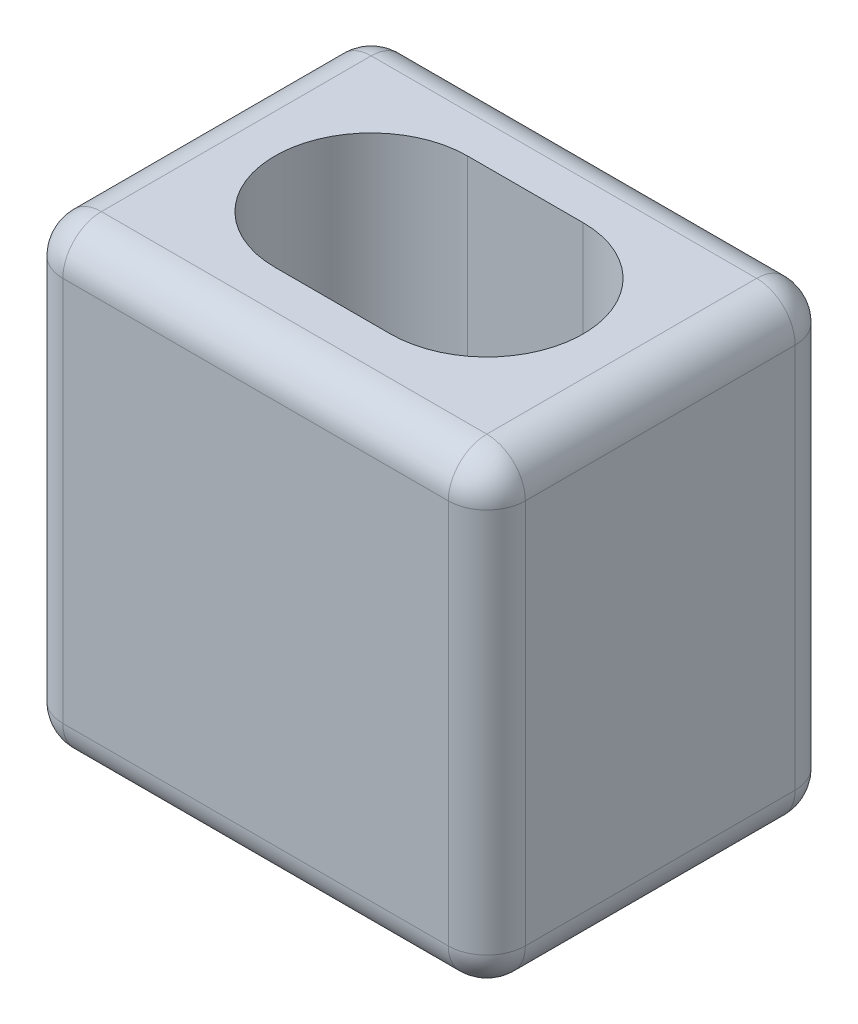
SolidWorks part; units mm, degrees
ref_plane "Front Plane" through (0, 0, 0) normal (0, 0, 1) x (1, 0, 0)
ref_plane "Top Plane" through (0, 0, 0) normal (0, 1, 0) x (1, 0, 0)
ref_plane "Right Plane" through (0, 0, 0) normal (1, 0, 0) x (0, 0, -1)
sketch "Sketch1" plane through (0, 0, 0) normal (0, 1, 0) x (1, 0, 0)
  line L0 (-19.05, 0) -> (19.05, 0) construction
  line L1 (-76.2, -57.15) -> (76.2, -57.15)
  line L2 (-76.2, -57.15) -> (-76.2, 57.15)
  line L3 (-76.2, 57.15) -> (76.2, 57.15)
  line L4 (76.2, -57.15) -> (76.2, 57.15)
  line L5 (-76.2, -57.15) -> (76.2, 57.15) construction
  line L6 (-76.2, 57.15) -> (76.2, -57.15) construction
  line L7 (-19.05, 31.75) -> (19.05, 31.75)
  line L8 (-19.05, -31.75) -> (19.05, -31.75)
  arc A0 (-19.05, 31.75) -> (-19.05, -31.75) centre (-19.05, 0) ccw
  arc A1 (19.05, -31.75) -> (19.05, 31.75) centre (19.05, 0) ccw
  point P0 (0, 0)
  point P8 (0, 0)
  dimension "D1" = 152.4
  dimension "D2" = 114.3
  dimension "D3" = 38.1
  dimension "D4" = 63.5
extrude "Boss-Extrude1" add sketch "Sketch1" along normal blind 152.4
sketch "Sketch7" plane through (-76.2, 0, 0) normal (-1, 0, 0) x (0, 0, 1)
  line L0 (-57.15, 76.2) -> (57.15, 76.2) construction
  line L1 (-57.15, 152.4) -> (-57.15, 0) construction
  line L2 (57.15, 152.4) -> (57.15, 0) construction
  line L3 (0, 152.4) -> (0, 0) construction
  line L4 (-57.15, 152.4) -> (57.15, 152.4) construction
  line L5 (0, 57.15) -> (0, 95.25) construction
  line L6 (-31.75, 57.15) -> (-31.75, 95.25)
  line L7 (31.75, 57.15) -> (31.75, 95.25)
  arc A0 (-31.75, 57.15) -> (31.75, 57.15) centre (0, 57.15) ccw
  arc A1 (31.75, 95.25) -> (-31.75, 95.25) centre (0, 95.25) ccw
  point P13 (0, 76.2)
  dimension "D1" = 38.1
  dimension "D2" = 63.5
fillet "Fillet1" radius 12.7 12 edges at (-76.2, 76.2, -57.15) (0, 0, -57.15) (76.2, 76.2, -57.15) (0, 152.4, -57.15) (0, 152.4, 57.15) (76.2, 76.2, 57.15) (0, 0, 57.15) (-76.2, 76.2, 57.15) (-76.2, 152.4, 0) (76.2, 152.4, 0) (76.2, 0, 0) (-76.2, 0, 0)
sketch "Sketch2" plane through (0, 0, -57.15) normal (0, 0, -1) x (-1, 0, 0)
  line L0 (0, 0) -> (0, 152.4) construction
  line L1 (-76.2, 0) -> (76.2, 0) construction
  line L2 (-76.2, 152.4) -> (76.2, 152.4) construction
  line L3 (-76.2, 76.2) -> (76.2, 76.2) construction
  line L4 (-76.2, 152.4) -> (-76.2, 0) construction
  line L5 (76.2, 152.4) -> (76.2, 0) construction
  line L6 (-19.05, 76.2) -> (19.05, 76.2) construction
  line L7 (-19.05, 107.95) -> (19.05, 107.95)
  line L8 (-19.05, 44.45) -> (19.05, 44.45)
  arc A0 (-19.05, 107.95) -> (-19.05, 44.45) centre (-19.05, 76.2) ccw
  arc A1 (19.05, 44.45) -> (19.05, 107.95) centre (19.05, 76.2) ccw
  point P14 (0, 76.2)
  dimension "D1" = 38.1
  dimension "D2" = 63.5
sketch "Sketch4" plane through (76.2, 0, 0) normal (1, 0, 0) x (0, 0, -1)
  line L0 (-57.15, 76.2) -> (57.15, 76.2) construction
  line L1 (-57.15, 152.4) -> (-57.15, 0) construction
  line L2 (0, 152.4) -> (0, 0) construction
  line L3 (-57.15, 152.4) -> (57.15, 152.4) construction
  line L4 (0, 57.15) -> (0, 95.25) construction
  line L5 (-31.75, 57.15) -> (-31.75, 95.25)
  line L6 (31.75, 57.15) -> (31.75, 95.25)
  arc A0 (-31.75, 57.15) -> (31.75, 57.15) centre (0, 57.15) ccw
  arc A1 (31.75, 95.25) -> (-31.75, 95.25) centre (0, 95.25) ccw
  point P12 (0, 76.2)
  dimension "D1" = 38.1
  dimension "D2" = 63.5
